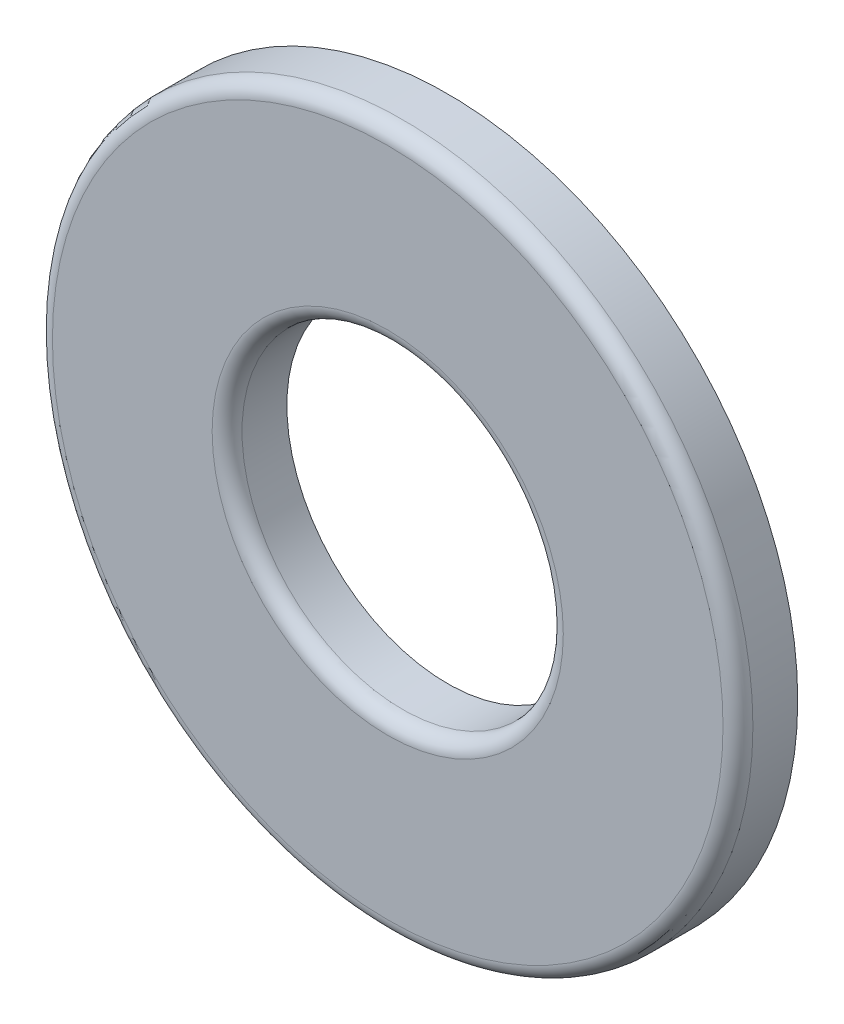
SolidWorks part; units mm, degrees
other "Imported1" parameters "D1"=0.2032, "TH"=1.0287, "Thickness"=0.8128
material "Alloy Steel (SS)"
ref_plane "Front Plane" through (0, 0, 0) normal (0, 0, 1) x (1, 0, 0)
ref_plane "Top Plane" through (0, 0, 0) normal (0, 1, 0) x (1, 0, 0)
ref_plane "Right Plane" through (0, 0, 0) normal (1, 0, 0) x (0, 0, -1)
sketch "Sketch1" plane through (0, 0, 0) normal (0, 0, 1) x (1, 0, 0)
  line L0 (-4.7625, 0) -> (4.7625, 0) construction
  line L1 (-2.1844, 0) -> (2.1844, 0) construction
  circle A0 centre (0, 0) radius 2.1844 construction
  circle A1 centre (0, 0) radius 4.7625 construction
  point P8 (0, 0)
  point P9 (0, 4.7625)
  point P11 (2.1844, 0)
  dimension "ID" = 4.3688
  dimension "OD" = 9.525
sketch "Sketch2" plane through (0, 0, 0) normal (1, 0, 0) x (0, 0, -1)
  line L0 (-0.4064, 4.7625) -> (0.4064, 4.7625) construction
  point P2 (0, 4.7625)
sketch "Sketch3" plane through (0, 0, 0) normal (0, 0, 1) x (1, 0, 0)
  circle A0 centre (0, 0) radius 2.1844
  circle A1 centre (0, 0) radius 4.7625
extrude "Boss-Extrude1" add sketch "Sketch3" along normal up to vertex (0.4064 mm away) and the other way up to vertex (0.4064 mm away) up to point (0, 4.7625, 0.4064) other way up to point (0, 4.7625, -0.4064)
fillet "Fillet1" radius 0.2032 2 edges at (4.7625, 0, 0.4064) (2.1844, 0, 0.4064)
equation "\"D1@Fillet1\"=\"Thickness@Sketch2\"/4"
